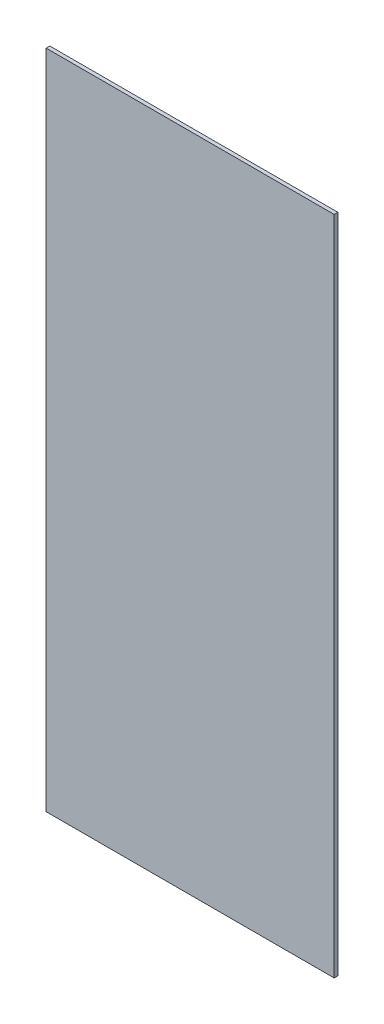
SolidWorks part; units mm, degrees
material "Acrylic (Medium-high impact)"
ref_plane "Front Plane" through (0, 0, 0) normal (0, 0, 1) x (1, 0, 0)
ref_plane "Top Plane" through (0, 0, 0) normal (0, 1, 0) x (1, 0, 0)
ref_plane "Right Plane" through (0, 0, 0) normal (1, 0, 0) x (0, 0, -1)
sketch "Sketch1" plane through (0, 0, 0) normal (0, 0, 1) x (1, 0, 0)
  line L1 (0, 0) -> (248.92, 0)
  line L2 (0, 0) -> (0, 571.5)
  line L3 (0, 571.5) -> (248.92, 571.5)
  line L4 (248.92, 0) -> (248.92, 571.5)
  dimension "D1" = 571.5
  dimension "D2" = 248.92
extrude "Boss-Extrude1" add sketch "Sketch1" along normal blind 3.175
